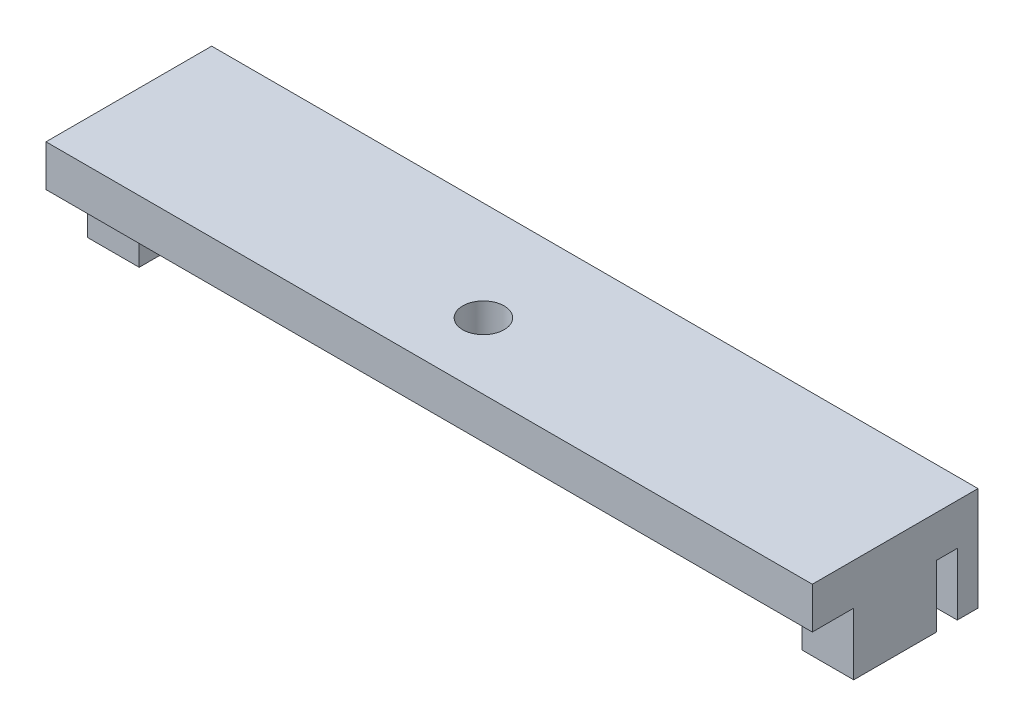
SolidWorks part; units mm, degrees
ref_plane "Front Plane" through (0, 0, 0) normal (0, 0, 1) x (1, 0, 0)
ref_plane "Top Plane" through (0, 0, 0) normal (0, 1, 0) x (1, 0, 0)
ref_plane "Right Plane" through (0, 0, 0) normal (1, 0, 0) x (0, 0, -1)
sketch "Sketch1" plane through (0, 0, 0) normal (0, 1, 0) x (1, 0, 0)
  line L1 (-18.5, -4) -> (18.5, -4)
  line L2 (-18.5, -4) -> (-18.5, 4)
  line L3 (-18.5, 4) -> (18.5, 4)
  line L4 (18.5, -4) -> (18.5, 4)
  line L5 (-18.5, -4) -> (18.5, 4) construction
  line L6 (-18.5, 4) -> (18.5, -4) construction
  point P0 (0, 0)
  dimension "D1" = 37
  dimension "D2" = 8
extrude "Boss-Extrude1" add sketch "Sketch1" along normal blind 2
sketch "Sketch2" plane through (0, 2, 0) normal (0, 1, 0) x (1, 0, 0)
  line L0 (-18.5, -4) -> (18.5, -4) construction
  line L1 (-18.5, 4) -> (-18.5, -4) construction
  circle A0 centre (-0.58, -0.8) radius 1
  dimension "D1" = 2
  dimension "D2" = 3.2
  dimension "D3" = 17.92
extrude "Cut-Extrude1" cut sketch "Sketch2" against normal through all
sketch "Sketch3" plane through (0, 0, 0) normal (0, -1, 0) x (1, 0, 0)
  line L0 (18.5, 4) -> (18.5, -4) construction
  line L1 (18.5, 2) -> (16, 2)
  line L2 (18.5, 2) -> (18.5, -2)
  line L3 (18.5, -2) -> (16, -2)
  line L4 (16, 2) -> (16, -2)
  line L5 (18.5, 2) -> (16, -2) construction
  line L6 (18.5, -2) -> (16, 2) construction
  line L8 (-18.5, 4) -> (18.5, 4) construction
  line L9 (18.5, -4) -> (-18.5, -4) construction
  line L10 (18.5, -3) -> (16, -3)
  line L11 (18.5, -3) -> (18.5, -4)
  line L12 (18.5, -4) -> (16, -4)
  line L13 (16, -3) -> (16, -4)
  line L14 (18.5, -3) -> (16, -4) construction
  line L15 (18.5, -4) -> (16, -3) construction
  line L16 (0, 5.1525) -> (0, -5.1525) construction
  line L17 (-18.5, -4) -> (-16, -4)
  line L18 (-16, -3) -> (-16, -4)
  line L19 (-18.5, -3) -> (-16, -3)
  line L20 (-18.5, -3) -> (-18.5, -4)
  line L21 (-18.5, -2) -> (-16, -2)
  line L22 (-16, 2) -> (-16, -2)
  line L23 (-18.5, 2) -> (-16, 2)
  line L24 (-18.5, 2) -> (-18.5, -2)
  point P4 (17.25, 0)
  point P13 (17.25, -3.5)
  point P20 (0, 0)
  dimension "D1" = 2
  dimension "D2" = 4
  dimension "D3" = 2.5
  dimension "D4" = 2.5
  dimension "D5" = 1
extrude "Boss-Extrude2" add sketch "Sketch3" along normal blind 3
